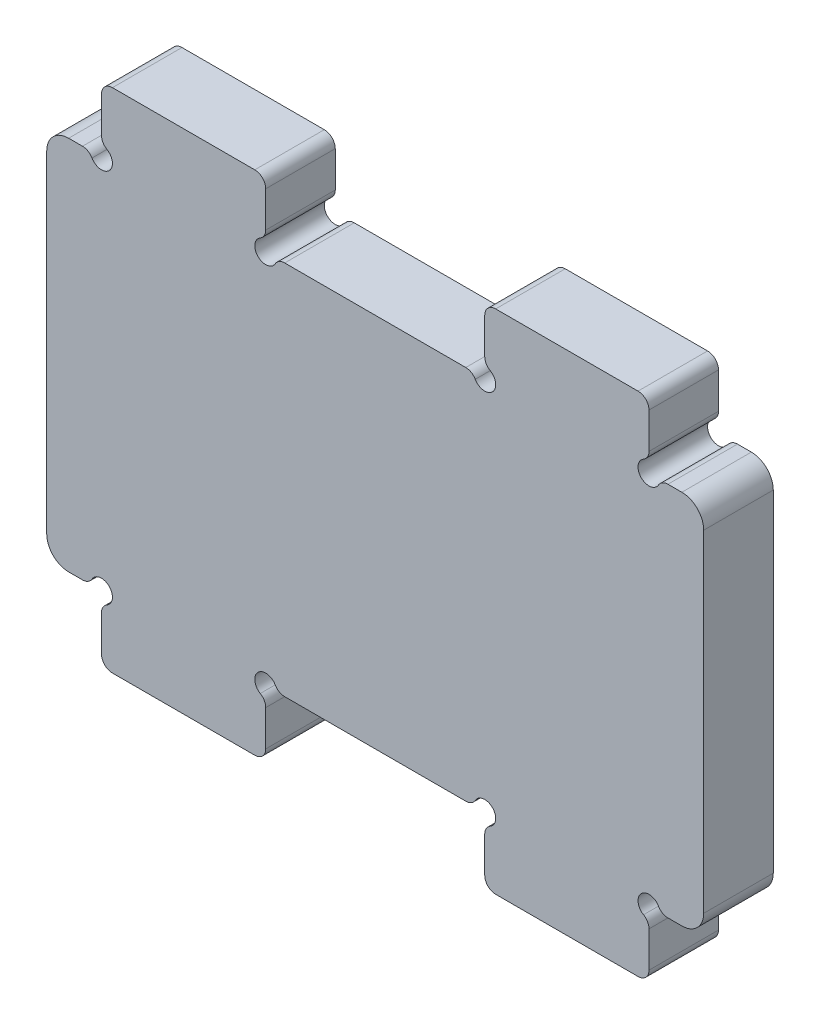
SolidWorks part; units mm, degrees
ref_plane "Front Plane" through (0, 0, 0) normal (0, 0, 1) x (1, 0, 0)
ref_plane "Top Plane" through (0, 0, 0) normal (0, 1, 0) x (1, 0, 0)
ref_plane "Right Plane" through (0, 0, 0) normal (1, 0, 0) x (0, 0, -1)
sketch "Sketch1" plane through (0, 0, 0) normal (0, 0, 1) x (1, 0, 0)
  line L0 (-30, 17.15) -> (30, 17.15)
  line L1 (-30, 17.15) -> (-30, -17.15)
  line L2 (30, 17.15) -> (30, -17.15)
  line L3 (-30, -17.15) -> (30, -17.15)
  line L4 (30, -17.15) -> (-30, 17.15) construction
  point P0 (0, 0)
  dimension "D1" = 60
  dimension "D2" = 34.3
extrude "Boss-Extrude1" add sketch "Sketch1" along normal blind 6.35
sketch "Sketch2" plane through (0, 0, 6.35) normal (0, 0, 1) x (1, 0, 0)
  line L0 (-25, 17.15) -> (-10, 17.15)
  line L1 (-25, 17.15) -> (-25, 23.15)
  line L2 (-10, 17.15) -> (-10, 23.15)
  line L3 (-25, 23.15) -> (-10, 23.15)
  line L4 (30, 17.15) -> (-30, 17.15) construction
  line L5 (-30, 17.15) -> (-30, -17.15) construction
  dimension "D1" = 5
  dimension "D2" = 15
  dimension "D3" = 6
extrude "Boss-Extrude2" add sketch "Sketch2" against normal up to surface (6.35 mm away) up to face at (0, 0, 0)
sketch "Sketch3" plane through (0, 0, 6.35) normal (0, 0, 1) x (1, 0, 0)
  circle A0 centre (-25, 17.15) radius 1
  circle A1 centre (-10, 17.15) radius 1
  dimension "D1" = 2
extrude "Cut-Extrude1" cut sketch "Sketch3" against normal through all
mirror "Mirror1" about plane through (0, 0, 0) normal (1, 0, 0) of "Boss-Extrude2", "Cut-Extrude1"
mirror "Mirror2" about plane through (0, 0, 0) normal (0, 1, 0) of "Mirror1", "Boss-Extrude2", "Cut-Extrude1"
fillet "Fillet1" radius 1 24 edges at (26, -17.15, 3.175) (25, -18.15, 3.175) (25, -23.15, 3.175) (10, -23.15, 3.175) (10, -18.15, 3.175) (9, -17.15, 3.175) (-9, -17.15, 3.175) (-10, -18.15, 3.175) (-10, -23.15, 3.175) (-25, -23.15, 3.175) (-25, -18.15, 3.175) (-26, -17.15, 3.175) (26, 17.15, 3.175) (25, 18.15, 3.175) (25, 23.15, 3.175) (10, 23.15, 3.175) (10, 18.15, 3.175) (9, 17.15, 3.175) (-9, 17.15, 3.175) (-10, 18.15, 3.175) (-10, 23.15, 3.175) (-25, 23.15, 3.175) (-25, 18.15, 3.175) (-26, 17.15, 3.175)
fillet "Fillet2" radius 2 4 edges at (30, -17.15, 3.175) (30, 17.15, 3.175) (-30, -17.15, 3.175) (-30, 17.15, 3.175)
